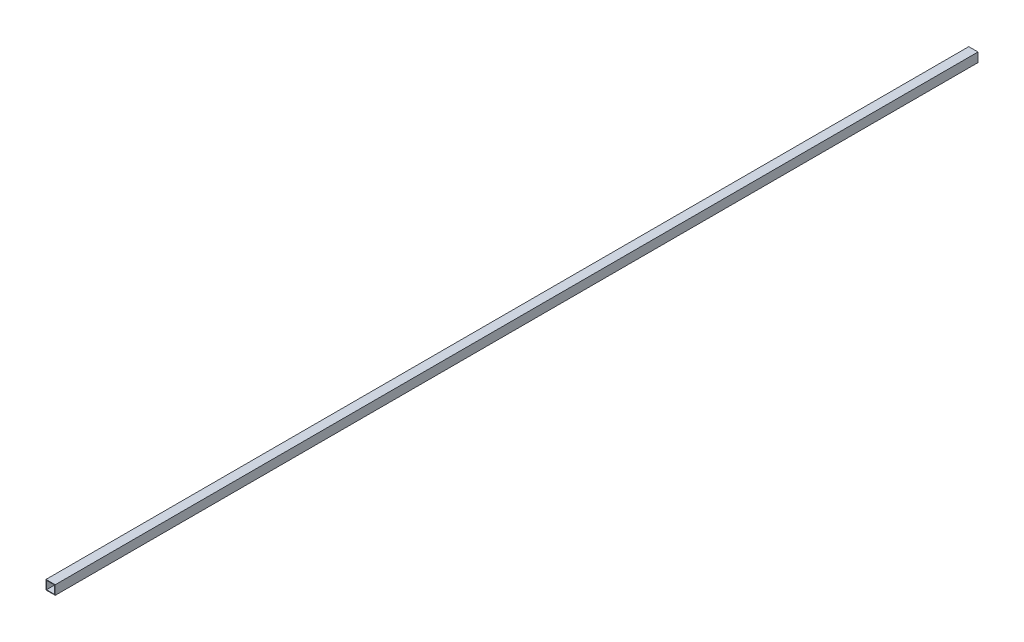
SolidWorks part; units mm, degrees
material "ALUMINUM 6061-T6"
ref_plane "Front Plane" through (0, 0, 0) normal (0, 0, 1) x (1, 0, 0)
ref_plane "Top Plane" through (0, 0, 0) normal (0, 1, 0) x (1, 0, 0)
ref_plane "Right Plane" through (0, 0, 0) normal (1, 0, 0) x (0, 0, -1)
sketch "Sketch1" plane through (0, 0, 0) normal (0, 0, 1) x (1, 0, 0)
  line L1 (-12.7, -12.7) -> (12.7, -12.7)
  line L2 (-12.7, -12.7) -> (-12.7, 12.7)
  line L3 (-12.7, 12.7) -> (12.7, 12.7)
  line L4 (12.7, -12.7) -> (12.7, 12.7)
  line L5 (-12.7, -12.7) -> (12.7, 12.7) construction
  line L6 (-12.7, 12.7) -> (12.7, -12.7) construction
  line L7 (11.1125, -11.1125) -> (-11.1125, -11.1125)
  line L8 (11.1125, -11.1125) -> (11.1125, 11.1125)
  line L9 (11.1125, 11.1125) -> (-11.1125, 11.1125)
  line L10 (-11.1125, -11.1125) -> (-11.1125, 11.1125)
  line L11 (11.1125, -11.1125) -> (-11.1125, 11.1125) construction
  line L12 (11.1125, 11.1125) -> (-11.1125, -11.1125) construction
  point P0 (0, 0)
  point P5 (0, 0)
  dimension "D1" = 25.4
  dimension "D2" = 25.4
  dimension "D3" = 1.5875
extrude "Boss-Extrude1" add sketch "Sketch1" along normal mid plane 2540
